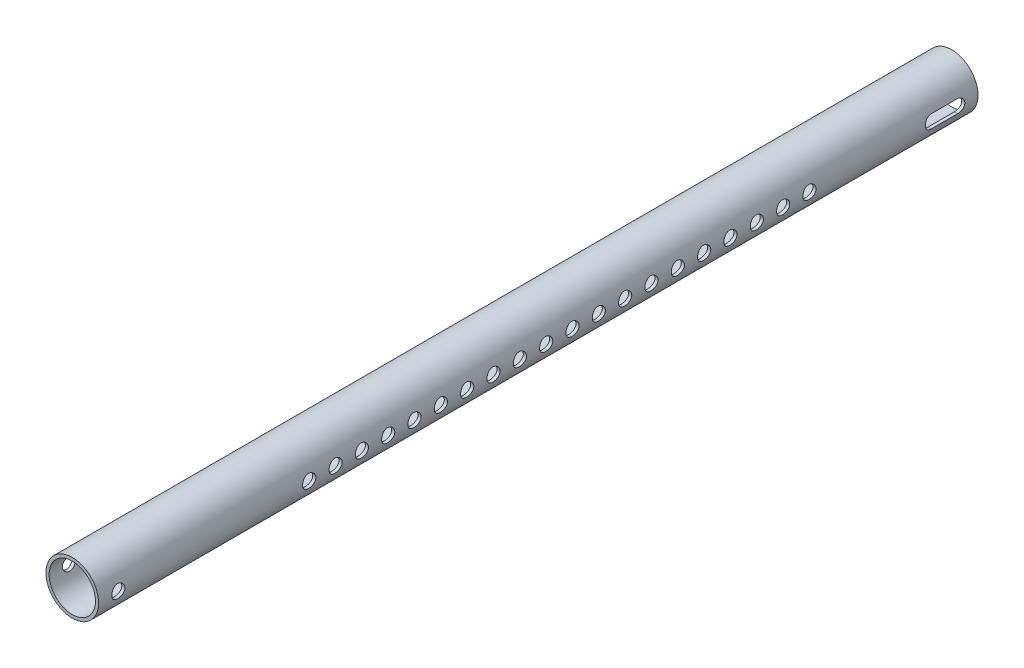
SolidWorks part; units mm, degrees
material "6061 Alloy"
ref_plane "Front Plane" through (0, 0, 0) normal (0, 0, 1) x (1, 0, 0)
ref_plane "Top Plane" through (0, 0, 0) normal (0, 1, 0) x (1, 0, 0)
ref_plane "Right Plane" through (0, 0, 0) normal (1, 0, 0) x (0, 0, -1)
sketch "Sketch1" plane through (0, 0, 0) normal (0, 0, 1) x (1, 0, 0)
  circle A0 centre (0, 0) radius 12.7
  circle A1 centre (0, 0) radius 11.176
  dimension "D1" = 25.4
  dimension "D2" = 1.524
extrude "Boss-Extrude1" add sketch "Sketch1" along normal blind 212.09 and the other way blind 212.09
sketch "Sketch2" plane through (0, 0, 0) normal (1, 0, 0) x (0, 0, -1)
  line L0 (-399.9493, 0) -> (23.585, 0) construction
  line L1 (-212.09, 12.7) -> (-212.09, -12.7) construction
  line L2 (189.865, 0) -> (202.565, 0) construction
  line L3 (189.865, 3.175) -> (202.565, 3.175)
  line L4 (189.865, -3.175) -> (202.565, -3.175)
  line L5 (212.09, -12.7) -> (212.09, 12.7) construction
  circle A0 centre (-110.49, 0) radius 3.175
  circle A1 centre (-97.79, 0) radius 3.175
  circle A2 centre (-85.09, 0) radius 3.175
  circle A3 centre (-72.39, 0) radius 3.175
  circle A4 centre (-59.69, 0) radius 3.175
  circle A5 centre (-46.99, 0) radius 3.175
  circle A6 centre (-34.29, 0) radius 3.175
  circle A7 centre (-21.59, 0) radius 3.175
  circle A8 centre (-8.89, 0) radius 3.175
  circle A9 centre (3.81, 0) radius 3.175
  circle A10 centre (16.51, 0) radius 3.175
  circle A11 centre (29.21, 0) radius 3.175
  circle A23 centre (41.91, 0) radius 3.175
  circle A24 centre (54.61, 0) radius 3.175
  circle A25 centre (67.31, 0) radius 3.175
  circle A26 centre (80.01, 0) radius 3.175
  circle A27 centre (92.71, 0) radius 3.175
  circle A28 centre (105.41, 0) radius 3.175
  circle A29 centre (118.11, 0) radius 3.175
  circle A30 centre (130.81, 0) radius 3.175
  circle A33 centre (-202.565, 0) radius 3.175
  arc A35 (189.865, 3.175) -> (189.865, -3.175) centre (189.865, 0) ccw
  arc A36 (202.565, -3.175) -> (202.565, 3.175) centre (202.565, 0) ccw
  point P35 (196.215, 0)
  dimension "D1" = 6.35
  dimension "D9" = 3.175
  dimension "D2" = 101.6
  dimension "D4" = 12.7
  dimension "D6" = 9.525
  dimension "D8" = 12.7
  dimension "D7" = 9.525
  dimension "D3" = 20
  dimension "D5" = 2
extrude "Cut-Extrude1" cut sketch "Sketch2" against normal through all and the other way through all
